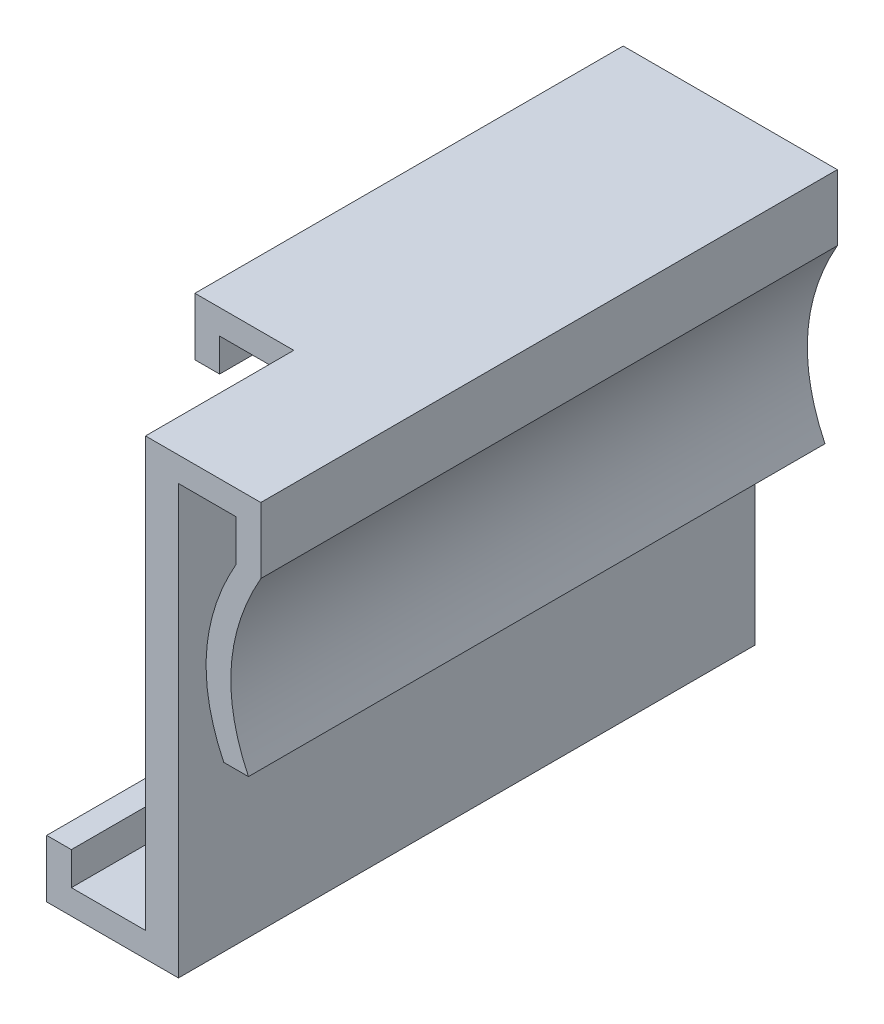
SolidWorks part; units mm, degrees
material "ABS"
ref_plane "Ebene vorne" through (0, 0, 0) normal (0, 0, 1) x (1, 0, 0)
ref_plane "Ebene oben" through (0, 0, 0) normal (0, 1, 0) x (1, 0, 0)
ref_plane "Ebene rechts" through (0, 0, 0) normal (1, 0, 0) x (0, 0, -1)
sketch "Skizze1" plane through (0, 0, 0) normal (0, 0, 1) x (1, 0, 0)
  line L0 (3.75, -1.0369) -> (5.25, -1.0369)
  line L1 (1, -13.75) -> (-1, -13.75)
  line L2 (1, -13.75) -> (1, 13.75)
  line L3 (1, 13.75) -> (-1, 13.75)
  line L4 (-1, -13.75) -> (-1, 13.75)
  line L5 (1, -13.75) -> (-1, 13.75) construction
  line L6 (1, 13.75) -> (-1, -13.75) construction
  line L7 (1, 13.75) -> (6, 13.75)
  line L8 (1, 13.75) -> (1, 12.25)
  line L9 (1, 12.25) -> (6, 12.25)
  line L10 (6, 13.75) -> (6, 12.25)
  line L11 (6, 12.25) -> (4.5, 12.25)
  line L12 (6, 12.25) -> (6, 9.75)
  line L13 (6, 9.75) -> (4.5, 9.75)
  line L14 (4.5, 12.25) -> (4.5, 9.75)
  line L16 (-1, 13.75) -> (-7, 13.75)
  line L17 (-1, 13.75) -> (-1, 12.25)
  line L18 (-1, 12.25) -> (-7, 12.25)
  line L19 (-7, 13.75) -> (-7, 12.25)
  line L20 (-7, 12.25) -> (-5.5, 12.25)
  line L21 (-7, 12.25) -> (-7, 10.25)
  line L22 (-7, 10.25) -> (-5.5, 10.25)
  line L23 (-5.5, 12.25) -> (-5.5, 10.25)
  line L24 (-1, -13.75) -> (-7, -13.75)
  line L25 (-1, -13.75) -> (-1, -12.25)
  line L26 (-1, -12.25) -> (-7, -12.25)
  line L27 (-7, -13.75) -> (-7, -12.25)
  line L28 (-7, -12.25) -> (-5.5, -12.25)
  line L29 (-7, -12.25) -> (-7, -10.25)
  line L30 (-7, -10.25) -> (-5.5, -10.25)
  line L31 (-5.5, -12.25) -> (-5.5, -10.25)
  spline S0 degree 2 poles (4.5, 9.75) (1.2829, 4.0957) (3.75, -1.0369) knots 0 0 0 1 1 1
  spline S1 degree 2 poles (6, 9.75) (2.7829, 4.0957) (5.25, -1.0369) knots 0 0 0 1 1 1
  point P0 (0, 0)
  dimension "D9" = 1.5
  dimension "D10" = 8.75
  dimension "D8" = 3.5
  dimension "D7" = 2
  dimension "D1" = 2
  dimension "D2" = 27.5
  dimension "D3" = 5
  dimension "D4" = 1.5
  dimension "D5" = 2.5
  dimension "D6" = 1.5
  dimension "D11" = 8.75
  dimension "D12" = 10.7869
  dimension "D13" = 6
  dimension "D14" = 2
  dimension "D15" = 1.5
  dimension "D16" = 6
  dimension "D17" = 2
  dimension "D18" = 1.5
  dimension "D19" = 1.5
  dimension "D20" = 1.5
extrude "Aufsatz-Linear austragen1" add sketch "Skizze1" along normal blind 35
sketch "Skizze3" plane through (0, 0, 35) normal (0, 0, 1) x (1, 0, 0)
  line L0 (-1, 12.25) -> (-1, 13.75)
  line L1 (6, 13.75) -> (-7, 13.75) construction
  line L2 (-1, 13.75) -> (-7, 13.75)
  line L3 (-7, 13.75) -> (-7, 10.25)
  line L4 (-7, 13.75) -> (-7, 10.25) construction
  line L5 (-7, 10.25) -> (-5.5, 10.25)
  line L6 (-5.5, 10.25) -> (-5.5, 12.25)
  line L7 (-5.5, 12.25) -> (-1, 12.25)
extrude "Schnitt-Linear austragen1" cut sketch "Skizze3" against normal blind 9
